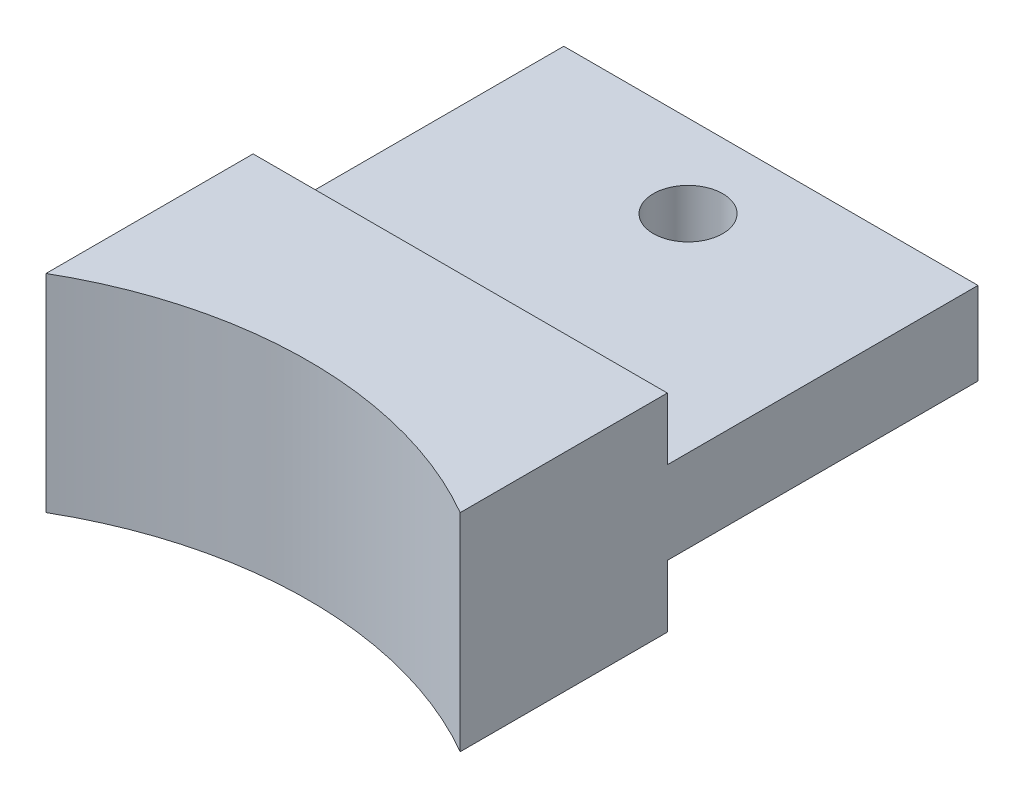
SolidWorks part; units mm, degrees
ref_plane "Front Plane" through (0, 0, 0) normal (0, 0, 1) x (1, 0, 0)
ref_plane "Top Plane" through (0, 0, 0) normal (0, 1, 0) x (1, 0, 0)
ref_plane "Right Plane" through (0, 0, 0) normal (1, 0, 0) x (0, 0, -1)
sketch "Sketch1" plane through (0, 0, 0) normal (0, 0, 1) x (1, 0, 0)
  line L1 (-10, -5) -> (10, -5)
  line L2 (-10, -5) -> (-10, 5)
  line L3 (-10, 5) -> (10, 5)
  line L4 (10, -5) -> (10, 5)
  line L5 (-10, -5) -> (10, 5) construction
  line L6 (-10, 5) -> (10, -5) construction
  point P0 (0, 0)
  dimension "D1" = 10
  dimension "D2" = 20
extrude "Boss-Extrude1" add sketch "Sketch1" along normal blind 10
sketch "Sketch2" plane through (0, 5, 0) normal (0, 1, 0) x (1, 0, 0)
  line L0 (-10, -10) -> (10, -10)
  arc A0 (-10, -10) -> (10, -10) centre (0, -27.3205) cw
  dimension "D1" = 20
extrude "Cut-Extrude1" cut sketch "Sketch2" against normal up to surface (10 mm away) up to face at (0, -5, 5)
sketch "Sketch3" plane through (0, 0, 0) normal (0, 0, -1) x (-1, 0, 0)
  line L0 (10, 5) -> (10, -5) construction
  line L1 (-10, -2) -> (10, -2)
  line L2 (-10, -2) -> (-10, 2)
  line L3 (-10, 2) -> (10, 2)
  line L4 (10, -2) -> (10, 2)
  line L5 (-10, -2) -> (10, 2) construction
  line L6 (-10, 2) -> (10, -2) construction
  point P0 (0, 0)
  dimension "D1" = 4
extrude "Boss-Extrude2" add sketch "Sketch3" along normal blind 15 contours L3 L4 L1 L2
hole_wizard "Tap Drill for M3x0.5 Tap6" positions "Sketch18" profile "Sketch19" hole size "M3x0.5" standard "ANSI Metric" end condition up to next
sketch "Sketch18" plane through (0, 2, 0) normal (0, 1, 0) x (1, 0, 0)
  line L2 (10, 15) -> (-10, 15) construction
  point P0 (0, 11)
  dimension "D1" = 4
sketch "Sketch19" plane through (0, 2, -11) normal (1, 0, 0) x (0, 0, 1)
  line L0 (0, 0) -> (0, 4)
  line L1 (0, 4) -> (1.675, 4)
  line L2 (1.675, 4) -> (1.675, 0)
  line L5 (1.675, 0) -> (0, 0)
  line L11 (0, -6.35) -> (0, 107.95) construction
  dimension "Thru Hole Dia." = 3.35
  dimension "Thru Hole Depth" = 4
